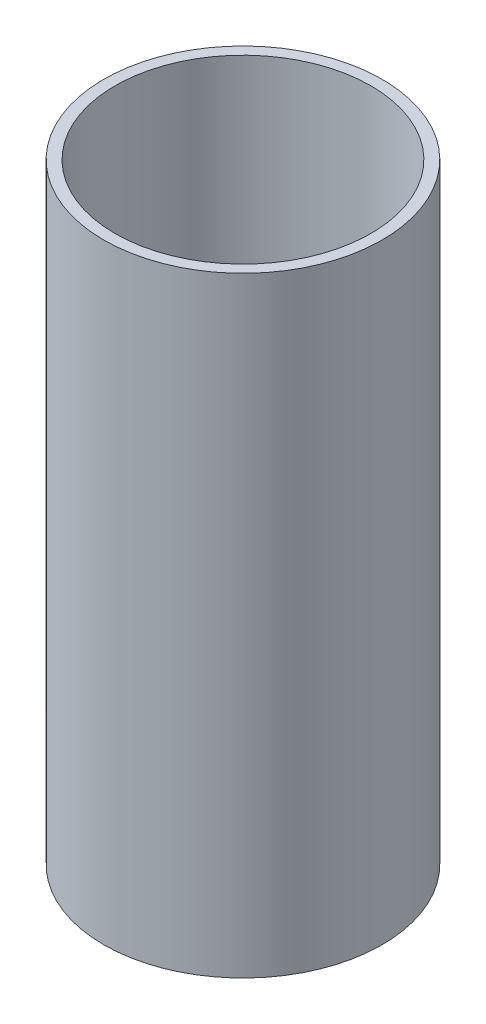
SolidWorks part; units mm, degrees
material "1.0035 (S185)"
ref_plane "Alzado" through (0, 0, 0) normal (0, 0, 1) x (1, 0, 0)
ref_plane "Planta" through (0, 0, 0) normal (0, 1, 0) x (1, 0, 0)
ref_plane "Vista lateral" through (0, 0, 0) normal (1, 0, 0) x (0, 0, -1)
sketch "Croquis3" plane through (0, 0, 0) normal (0, 0, 1) x (1, 0, 0)
  line L0 (0, 30.2199) -> (0, -83.7801) construction
  line L1 (-23.9, 30.2199) -> (-23.9, -83.7801)
  line L2 (-26, 30.2199) -> (-23.9, 30.2199)
  line L3 (-26, -83.7801) -> (-23.9, -83.7801)
  line L8 (-26, 30.2199) -> (-26, -83.7801)
  dimension "D2" = 26
  dimension "D3" = 2.1
  dimension "D10" = 114
revolve "Revolución1" add sketch "Croquis3" angle 360 about L0
